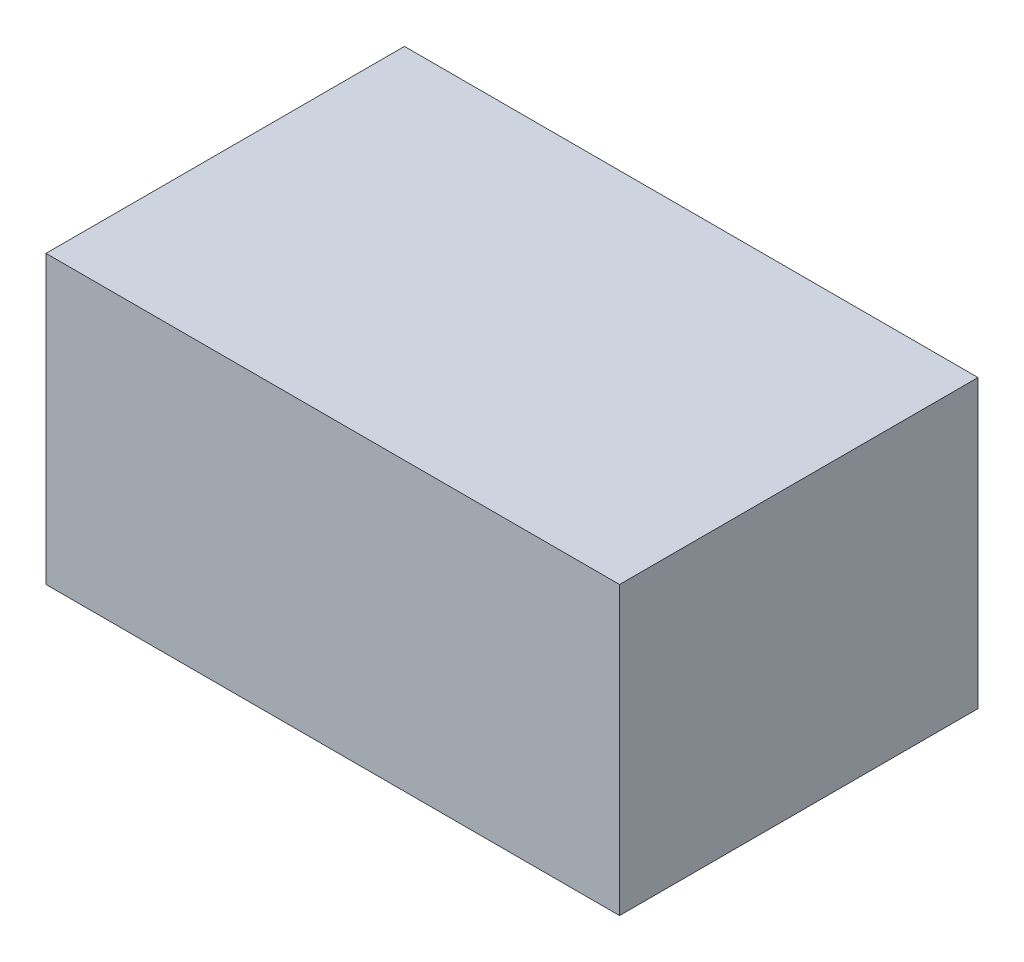
SolidWorks part; units mm, degrees
material "ABS"
ref_plane "Front Plane" through (0, 0, 0) normal (0, 0, 1) x (1, 0, 0)
ref_plane "Top Plane" through (0, 0, 0) normal (0, 1, 0) x (1, 0, 0)
ref_plane "Right Plane" through (0, 0, 0) normal (1, 0, 0) x (0, 0, -1)
sketch "Sketch2" plane through (0, 0, 0) normal (0, 1, 0) x (1, 0, 0)
  line L1 (40, 25) -> (-40, 25)
  line L2 (40, 25) -> (40, -25)
  line L3 (40, -25) -> (-40, -25)
  line L4 (-40, 25) -> (-40, -25)
  line L5 (40, 25) -> (-40, -25) construction
  line L6 (40, -25) -> (-40, 25) construction
  point P0 (0, 0)
  dimension "D1" = 50
  dimension "D2" = 80
extrude "Boss-Extrude1" add sketch "Sketch2" along normal blind 40
sketch "Sketch3" plane through (0, 0, 0) normal (0, -1, 0) x (1, 0, 0)
  line L12 (-34, 19) -> (-34, -19)
  line L13 (-34, -19) -> (34, -19)
  line L14 (34, -19) -> (34, 19)
  line L15 (34, 19) -> (-34, 19)
  line L16 (-34, 19) -> (-34, -19)
  line L17 (-34, -19) -> (34, -19)
  line L18 (34, -19) -> (34, 19)
  line L19 (34, 19) -> (-34, 19)
  dimension "D1" = 6
extrude "Cut-Extrude1" cut sketch "Sketch3" against normal blind 6
